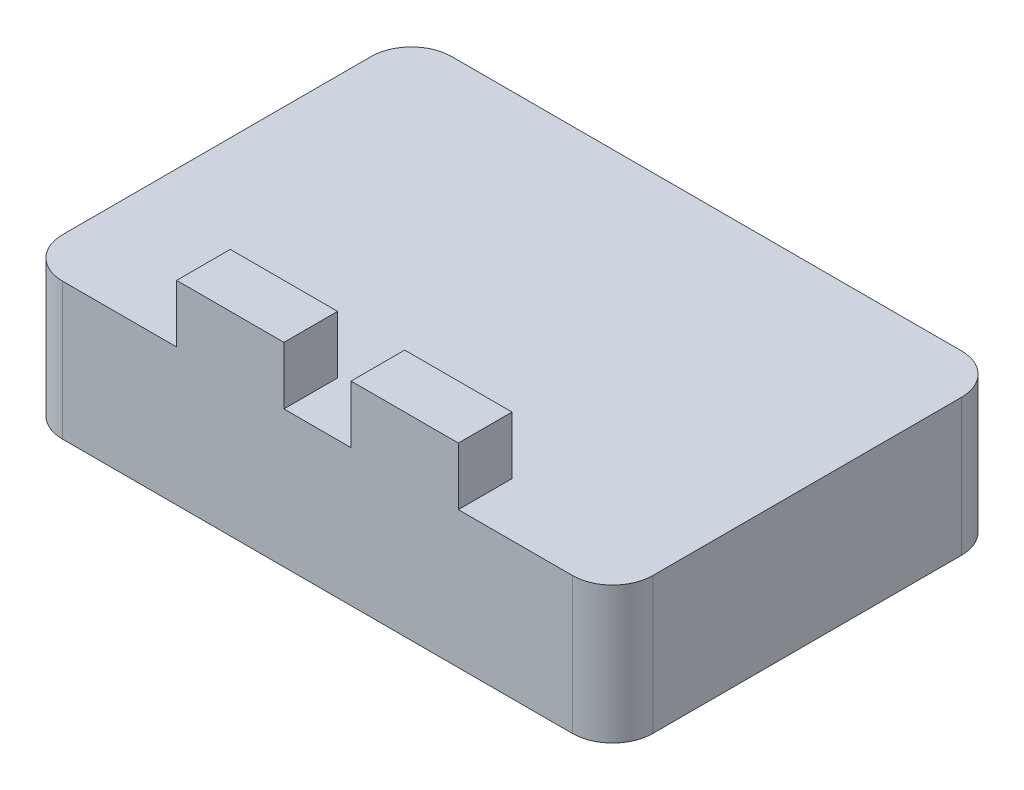
SolidWorks part; units mm, degrees
ref_plane "Front Plane" through (0, 0, 0) normal (0, 0, 1) x (1, 0, 0)
ref_plane "Top Plane" through (0, 0, 0) normal (0, 1, 0) x (1, 0, 0)
ref_plane "Right Plane" through (0, 0, 0) normal (1, 0, 0) x (0, 0, -1)
sketch "Sketch1" plane through (0, 0, 0) normal (0, 1, 0) x (1, 0, 0)
  line L1 (0, 0) -> (44, 0)
  line L2 (0, 0) -> (0, 29)
  line L3 (0, 29) -> (44, 29)
  line L4 (44, 0) -> (44, 29)
  dimension "D1" = 44
  dimension "D2" = 29
extrude "Boss-Extrude1" add sketch "Sketch1" along normal blind 10.2
sketch "Sketch2" plane through (0, 10.2, 0) normal (0, 1, 0) x (1, 0, 0)
  line L0 (22, 0) -> (22, 29) construction
  line L1 (0, 0) -> (44, 0) construction
  line L2 (44, 29) -> (0, 29) construction
  line L3 (19.5, 0) -> (24.5, 0) construction
  line L4 (24.5, 4) -> (32.5, 4)
  line L5 (19.5, 0) -> (11.5, 0)
  line L6 (19.5, 0) -> (19.5, 4)
  line L7 (19.5, 4) -> (11.5, 4)
  line L8 (11.5, 0) -> (11.5, 4)
  line L9 (32.5, 0) -> (32.5, 4)
  line L10 (24.5, 0) -> (32.5, 0)
  line L11 (24.5, 0) -> (24.5, 4)
  point P9 (22, 0)
  dimension "D1" = 5
  dimension "D2" = 8
  dimension "D3" = 4
extrude "Boss-Extrude2" add sketch "Sketch2" along normal blind 4.3
fillet "Fillet1" radius 3 4 edges at (44, 5.1, -29) (0, 5.1, -29) (0, 5.1, 0) (44, 5.1, 0)
